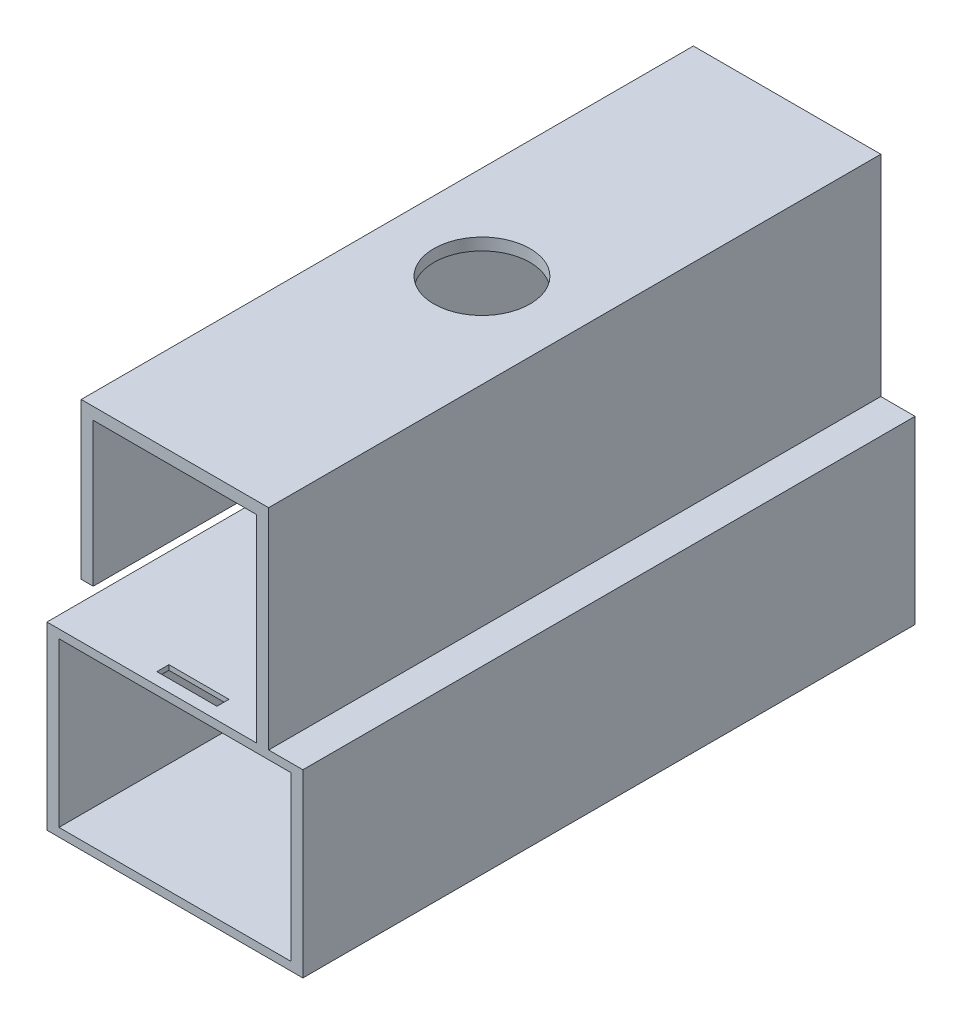
SolidWorks part; units mm, degrees
ref_plane "Front Plane" through (0, 0, 0) normal (0, 0, 1) x (1, 0, 0)
ref_plane "Top Plane" through (0, 0, 0) normal (0, 1, 0) x (1, 0, 0)
ref_plane "Right Plane" through (0, 0, 0) normal (1, 0, 0) x (0, 0, -1)
sketch "Sketch1" plane through (0, 0, 0) normal (0, 0, 1) x (1, 0, 0)
  line L1 (-21.3, 15.0093) -> (21.3, 15.0093)
  line L2 (-21.3, 15.0093) -> (-21.3, -15.0093)
  line L3 (-21.3, -15.0093) -> (21.3, -15.0093)
  line L4 (21.3, 15.0093) -> (21.3, -15.0093)
  line L5 (-21.3, 15.0093) -> (21.3, -15.0093) construction
  line L6 (-21.3, -15.0093) -> (21.3, 15.0093) construction
  line L7 (-19.3, 13.6) -> (19.3, 13.6)
  line L8 (-19.3, 13.6) -> (-19.3, -13.6)
  line L9 (-19.3, -13.6) -> (19.3, -13.6)
  line L10 (19.3, 13.6) -> (19.3, -13.6)
  line L11 (-19.3, 13.6) -> (19.3, -13.6) construction
  line L12 (-19.3, -13.6) -> (19.3, 13.6) construction
  point P0 (0, 0)
  point P6 (0, 0)
  dimension "D1" = 2
  dimension "D2" = 27.2
  dimension "D3" = 38.6
extrude "Boss-Extrude1" add sketch "Sketch1" along normal blind 101.9
sketch "Sketch3" plane through (0, 0, 0) normal (1, 0, 0) x (0, 0, -1)
  line L0 (-101.9, 15.0093) -> (0, 15.0093) construction
  line L1 (-12, 15.0093) -> (0, 15.0093)
  line L2 (-101.9, 15.0093) -> (0, 15.0093) construction
  line L3 (-12, 23.9054) -> (-12, 15.0093)
  line L4 (-101.9, 27) -> (-101.9, 56.6914) construction
  line L5 (0, 15.0093) -> (0, 49.9393)
  line L6 (0, 49.9393) -> (-101.9, 49.9393)
  line L7 (-101.9, 47.9393) -> (-12, 47.9393)
  line L8 (-12, 47.9393) -> (-12, 45.6407)
  line L9 (-101.9, 49.9393) -> (-101.9, 47.9393)
  arc A0 (-10.3883, 25.8673) -> (-9.3008, 41.8582) centre (-12, 34.0093) ccw
  arc A1 (-10.3883, 25.8673) -> (-12, 23.9054) centre (-10, 23.9054) ccw
  arc A2 (-9.3008, 41.8582) -> (-12, 45.6407) centre (-8, 45.6407) cw
  point P14 (-12, 25.7093)
  point P19 (-12, 42.3093)
  dimension "D1" = 16.6
  dimension "D3" = 2.2986
  dimension "D6" = 2
  dimension "D7" = 4
  dimension "D2" = 19
  dimension "D4" = 2
  dimension "D5" = 12
extrude "Boss-Extrude2" add sketch "Sketch3" along normal blind 13.6 and the other way blind 13.6 contours A0 L3 L1 L5 L6 L9 L7 L8
sketch "Sketch4" plane through (0, 0, 0) normal (0, 0, -1) x (-1, 0, 0)
  line L0 (13.6, 15.0093) -> (13.6, 49.9393) construction
  line L1 (-13.6, 15.0093) -> (-13.6, 49.9393) construction
  line L2 (13.6, 15.0093) -> (13.6, 49.9393)
  line L3 (-13.6, 15.0093) -> (-13.6, 49.9393)
  line L4 (-13.6, 49.9393) -> (-15.6, 49.9393)
  line L5 (-15.6, 49.9393) -> (-15.6, 15.0093)
  line L6 (-21.3, 15.0093) -> (-13.6, 15.0093) construction
  line L7 (-15.6, 15.0093) -> (-13.6, 15.0093)
  line L8 (13.6, 49.9393) -> (15.6, 49.9393)
  line L9 (15.6, 49.9393) -> (15.6, 15.0093)
  line L10 (13.6, 15.0093) -> (21.3, 15.0093) construction
  line L11 (15.6, 15.0093) -> (13.6, 15.0093)
  dimension "D1" = 2
extrude "Boss-Extrude3" add sketch "Sketch4" against normal up to surface (101.9 mm away) up to face at (0, 48.9393, 101.9)
sketch "Sketch5" plane through (0, 49.9393, 0) normal (0, 1, 0) x (1, 0, 0)
  line L0 (-13.6, -10.3883) -> (13.6, -10.3883) construction
  line L4 (-13.6, -10.3883) -> (13.6, -10.3883) construction
  line L6 (0, -16.5103) -> (0, 16.5103) construction
  circle A0 centre (0, -50.7883) radius 8
  dimension "D1" = 40.4
  dimension "D2" = 16
extrude "Cut-Extrude1" cut sketch "Sketch5" against normal up to surface (2 mm away) up to face at (0, 47.9393, 56.95)
sketch "Sketch6" plane through (0, 13.6, 0) normal (0, -1, 0) x (1, 0, 0)
  line L0 (19.3, 101.9) -> (-19.3, 101.9) construction
  line L1 (5, 97.9) -> (-5, 97.9)
  line L2 (5, 97.9) -> (5, 99.9)
  line L3 (5, 99.9) -> (-5, 99.9)
  line L4 (-5, 97.9) -> (-5, 99.9)
  line L5 (5, 97.9) -> (-5, 99.9) construction
  line L6 (5, 99.9) -> (-5, 97.9) construction
  line L7 (0, -16.5103) -> (0, 16.5103) construction
  point P0 (0, 98.9)
  dimension "D1" = 2
  dimension "D2" = 2
  dimension "D3" = 10
extrude "Cut-Extrude2" cut sketch "Sketch6" against normal up to next
sketch "Sketch7" plane through (0, 13.6, 0) normal (0, -1, 0) x (1, 0, 0)
  line L0 (5, 99.9) -> (-5, 99.9) construction
  line L1 (-5, 99.9) -> (-5, 97.9) construction
  line L2 (-5, 97.9) -> (5, 97.9) construction
  line L3 (5, 97.9) -> (5, 99.9) construction
  line L4 (5, 99.9) -> (-5, 99.9)
  line L5 (-5, 99.9) -> (-5, 97.9)
  line L6 (-5, 97.9) -> (5, 97.9)
  line L7 (5, 97.9) -> (5, 99.9)
  line L8 (-6, 96.9) -> (6, 96.9)
  line L9 (6, 96.9) -> (6, 100.9)
  line L10 (6, 100.9) -> (-6, 100.9)
  line L11 (-6, 100.9) -> (-6, 96.9)
  dimension "D1" = 1
extrude "Cut-Extrude3" cut sketch "Sketch7" against normal blind 0.6
sketch "Sketch8" plane through (0, 0, 101.9) normal (0, 0, 1) x (1, 0, 0)
  line L0 (-13.6, 15.0093) -> (-15.6, 15.0093)
  line L1 (-15.6, 15.0093) -> (-15.6, 24.0093)
  line L2 (-15.6, 15.0093) -> (-15.6, 49.9393) construction
  line L3 (-15.6, 24.0093) -> (-13.6, 24.0093)
  line L4 (-13.6, 47.9393) -> (-13.6, 15.0093) construction
  line L5 (-13.6, 24.0093) -> (-13.6, 15.0093)
  dimension "D1" = 9
extrude "Cut-Extrude4" cut sketch "Sketch8" against normal blind 70
